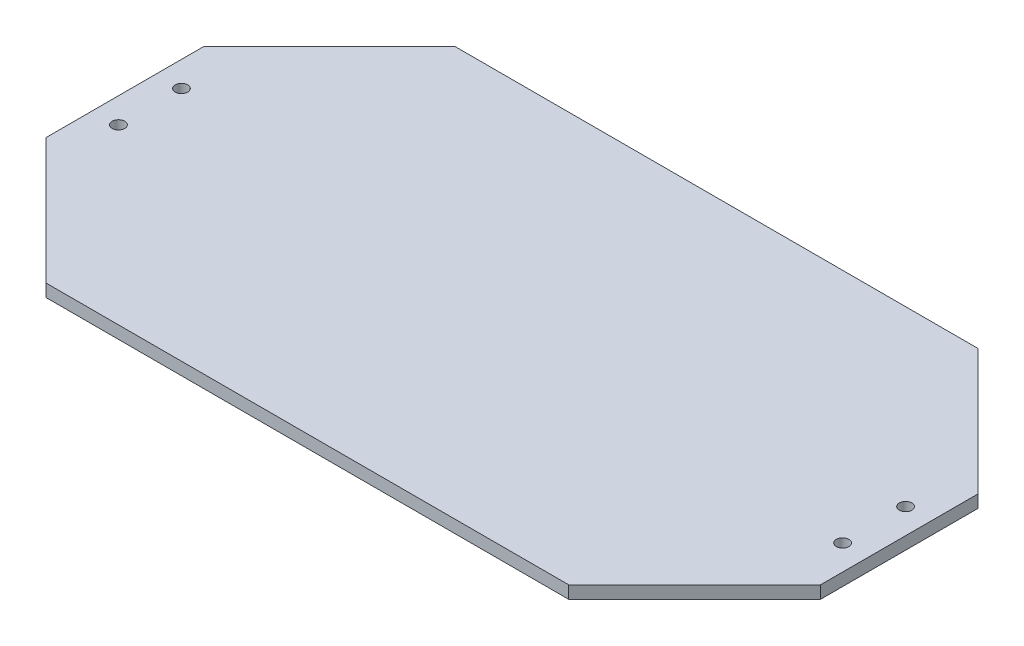
SolidWorks part; units mm, degrees
ref_plane "Front" through (0, 0, 0) normal (0, 0, 1) x (1, 0, 0)
ref_plane "Top" through (0, 0, 0) normal (0, 1, 0) x (1, 0, 0)
ref_plane "Right" through (0, 0, 0) normal (1, 0, 0) x (0, 0, -1)
sketch "Sketch1" plane through (0, 0, 0) normal (0, 1, 0) x (1, 0, 0)
  line L0 (-1.3988, 0) -> (32.4134, 0) construction
  line L1 (-10.16, 31.75) -> (-10.16, -31.75)
  line L2 (-10.16, -31.75) -> (40.64, -82.55)
  line L3 (40.64, -82.55) -> (251.46, -82.55)
  line L4 (251.46, -82.55) -> (302.26, -31.75)
  line L5 (302.26, -31.75) -> (302.26, 31.75)
  line L6 (302.26, 31.75) -> (251.46, 82.55)
  line L7 (251.46, 82.55) -> (40.64, 82.55)
  line L8 (40.64, 82.55) -> (-10.16, 31.75)
  line L9 (146.05, 82.55) -> (146.05, -131.0541) construction
  circle A0 centre (0, -12.7) radius 2.54
  circle A1 centre (292.1, -12.7) radius 2.54
  circle A2 centre (0, 12.7) radius 2.54
  circle A3 centre (292.1, 12.7) radius 2.54
  dimension "D1" = 5.08
  dimension "D2" = 25.4
  dimension "D3" = 5.08
  dimension "D5" = 292.1
  dimension "D4" = 25.4
  dimension "D6" = 63.5
  dimension "D7" = 10.16
  dimension "D8" = 165.1
  dimension "D9" = 50.8
  dimension "D10" = 50.8
  dimension "D11" = 10.16
  dimension "D12" = 63.5
extrude "Boss-Extrude1" add sketch "Sketch1" along normal blind 5.08 contours L7 L8 L1 L2 L3 L4 L5 L6 | A0 | A2 | A3 | A1
